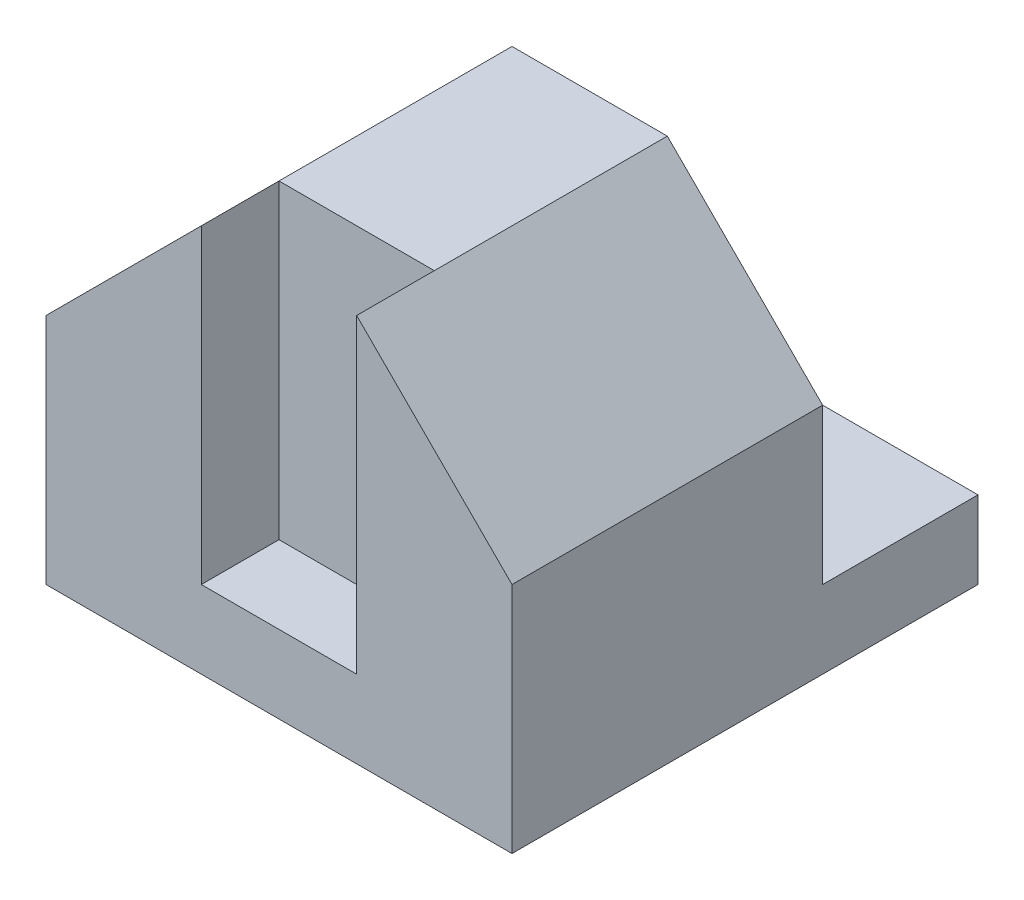
SolidWorks part; units mm, degrees
ref_plane "Front Plane" through (0, 0, 0) normal (0, 0, 1) x (1, 0, 0)
ref_plane "Top Plane" through (0, 0, 0) normal (0, 1, 0) x (1, 0, 0)
ref_plane "Right Plane" through (0, 0, 0) normal (1, 0, 0) x (0, 0, -1)
sketch "Sketch2" plane through (0, 0, 0) normal (0, 1, 0) x (1, 0, 0)
  line L1 (-3, -3) -> (3, -3)
  line L2 (-3, -3) -> (-3, 3)
  line L3 (-3, 3) -> (3, 3)
  line L4 (3, -3) -> (3, 3)
  line L5 (-3, -3) -> (3, 3) construction
  line L6 (-3, 3) -> (3, -3) construction
  point P0 (0, 0)
  dimension "D1" = 6
  dimension "D2" = 6
extrude "Boss-Extrude1" add sketch "Sketch2" along normal blind 5
sketch "Sketch3" plane through (3, 0, 0) normal (1, 0, 0) x (0, 0, -1)
  line L0 (-3, 0) -> (3, 0) construction
  line L1 (3, 5) -> (1, 5)
  line L2 (3, 5) -> (3, 1)
  line L3 (3, 1) -> (1, 1)
  line L4 (1, 5) -> (1, 1)
  dimension "D1" = 1
  dimension "D2" = 2
extrude "Cut-Extrude1" cut sketch "Sketch3" against normal blind 8
sketch "Sketch4" plane through (0, 0, 3) normal (0, 0, 1) x (1, 0, 0)
  line L0 (-3, 3) -> (-1, 5)
  line L1 (-3, 5) -> (-3, 0) construction
  line L2 (-1, 5) -> (-3, 5)
  line L3 (-3, 5) -> (-3, 3)
  line L4 (1, 5) -> (3, 5)
  line L5 (-3, 5) -> (3, 5) construction
  line L6 (3, 5) -> (3, 3)
  line L7 (3, 5) -> (3, 0) construction
  line L8 (3, 3) -> (1, 5)
  dimension "D1" = 2
  dimension "D2" = 2
  dimension "D3" = 2
  dimension "D4" = 2
extrude "Cut-Extrude2" cut sketch "Sketch4" against normal blind 8
sketch "Sketch5" plane through (0, 0, 3) normal (0, 0, 1) x (1, 0, 0)
  line L1 (-1, 1) -> (1, 1)
  line L2 (-1, 1) -> (-1, 5)
  line L3 (-1, 5) -> (1, 5)
  line L4 (1, 1) -> (1, 5)
  dimension "D1" = 0
  dimension "D2" = 2
  dimension "D3" = 4
extrude "Cut-Extrude3" cut sketch "Sketch5" against normal blind 1
